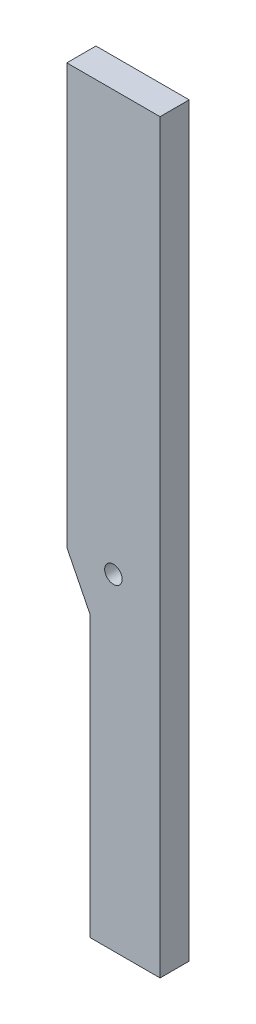
SolidWorks part; units mm, degrees
ref_plane "Front Plane" through (0, 0, 0) normal (0, 0, 1) x (1, 0, 0)
ref_plane "Top Plane" through (0, 0, 0) normal (0, 1, 0) x (1, 0, 0)
ref_plane "Right Plane" through (0, 0, 0) normal (1, 0, 0) x (0, 0, -1)
sketch "Sketch1" plane through (0, 0, 0) normal (0, 0, 1) x (1, 0, 0)
  line L1 (50.8, 0) -> (0, 0)
  line L2 (0, 0) -> (0, 254)
  line L3 (0, 254) -> (50.8, 254)
  line L4 (50.8, 0) -> (50.8, 254)
  dimension "D1" = 254
  dimension "D2" = 50.8
extrude "Boss-Extrude1" add sketch "Sketch1" along normal blind 15.875
chamfer "Chamfer1" distance 25.4 distance2 12.7 1 edges at (0, 0, 7.9375)
sketch "Sketch2" plane through (0, 0, 15.875) normal (0, 0, 1) x (1, 0, 0)
  line L0 (25.4, 254) -> (25.4, 0) construction
  line L1 (50.8, 254) -> (0, 254) construction
  line L2 (12.7, 0) -> (50.8, 0) construction
  line L3 (0, 25.4) -> (25.4, 25.4) construction
  circle A0 centre (25.4, 25.4) radius 4.7625
  dimension "D1" = 9.525
extrude "Cut-Extrude1" cut sketch "Sketch2" against normal through all
sketch "Sketch3" plane through (0, 0, 15.875) normal (0, 0, 1) x (1, 0, 0)
  line L0 (50.8, 0) -> (50.8, 254) construction
  line L1 (12.7, 0) -> (50.8, 0)
  line L2 (12.7, 0) -> (12.7, -152.4)
  line L3 (12.7, -152.4) -> (50.8, -152.4)
  line L4 (50.8, 0) -> (50.8, -152.4)
  dimension "D1" = 152.4
extrude "Boss-Extrude2" add sketch "Sketch3" against normal blind 15.875
